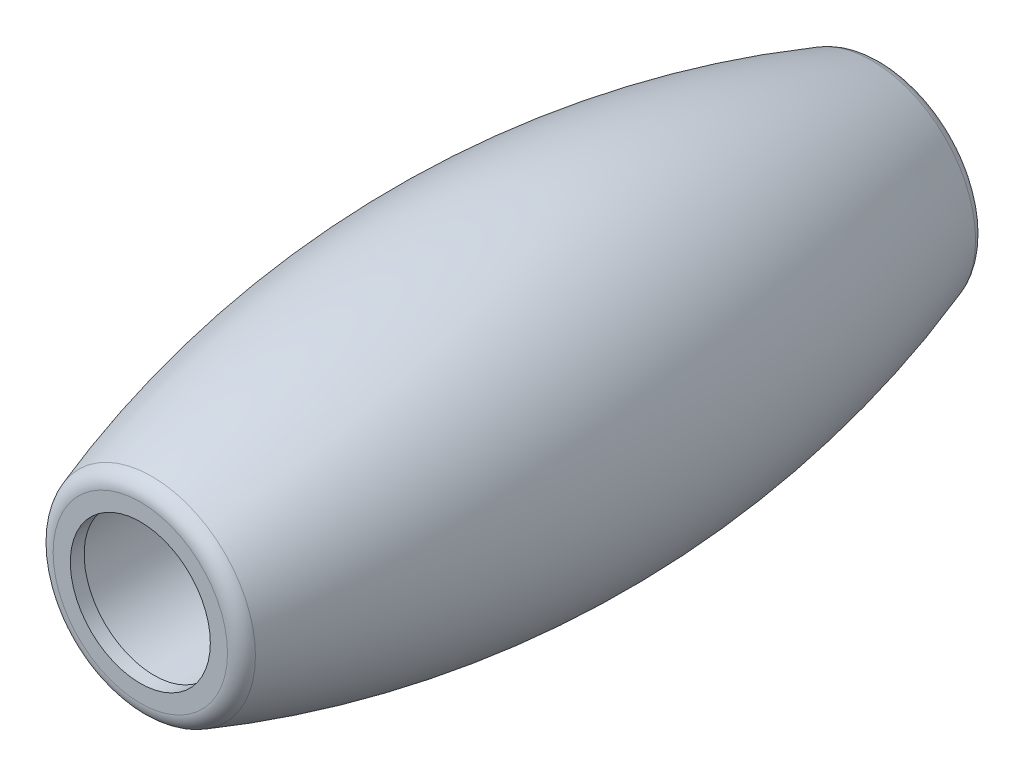
SolidWorks part; units mm, degrees
material "BUTYL"
ref_plane "Front Plane" through (0, 0, 0) normal (0, 0, 1) x (1, 0, 0)
ref_plane "Top Plane" through (0, 0, 0) normal (0, 1, 0) x (1, 0, 0)
ref_plane "Right Plane" through (0, 0, 0) normal (1, 0, 0) x (0, 0, -1)
sketch "Sketch1" plane through (0, 0, 0) normal (1, 0, 0) x (0, 0, -1)
  line L0 (-21.5, 0) -> (21.5, 0) construction
  line L1 (21.5, 0) -> (21.5, 5.75) construction
  line L2 (-21.5, 0) -> (-21.5, 5.75) construction
  line L3 (21.5, 5.75) -> (21.5, 4.05)
  line L4 (20.7, 4.5) -> (-20.7, 4.5)
  line L5 (-21.5, 4.05) -> (-21.5, 5.75)
  line L6 (20.7, 4.5) -> (20.7, 4.05)
  line L7 (20.7, 4.05) -> (21.5, 4.05)
  line L8 (-20.7, 4.5) -> (-20.7, 4.05)
  line L9 (-20.7, 4.05) -> (-21.5, 4.05)
  line L10 (0, 4.5) -> (0, 9.5) construction
  arc A0 (21.5, 5.75) -> (-21.5, 5.75) centre (0, -54.0083) ccw
  dimension "D1" = 21.5
  dimension "D2" = 5
  dimension "D4" = 4.5
  dimension "D5" = 4.05
  dimension "D6" = 0.8
revolve "Revolve1" add sketch "Sketch1" angle 360 about L0
fillet "Fillet1" radius 1 2 edges at (5.75, 0, -21.5) (5.75, 0, 21.5)
scale "Scale1" bodies to scale 101 scale about centroid uniform scaling yes scale factor 0.6
